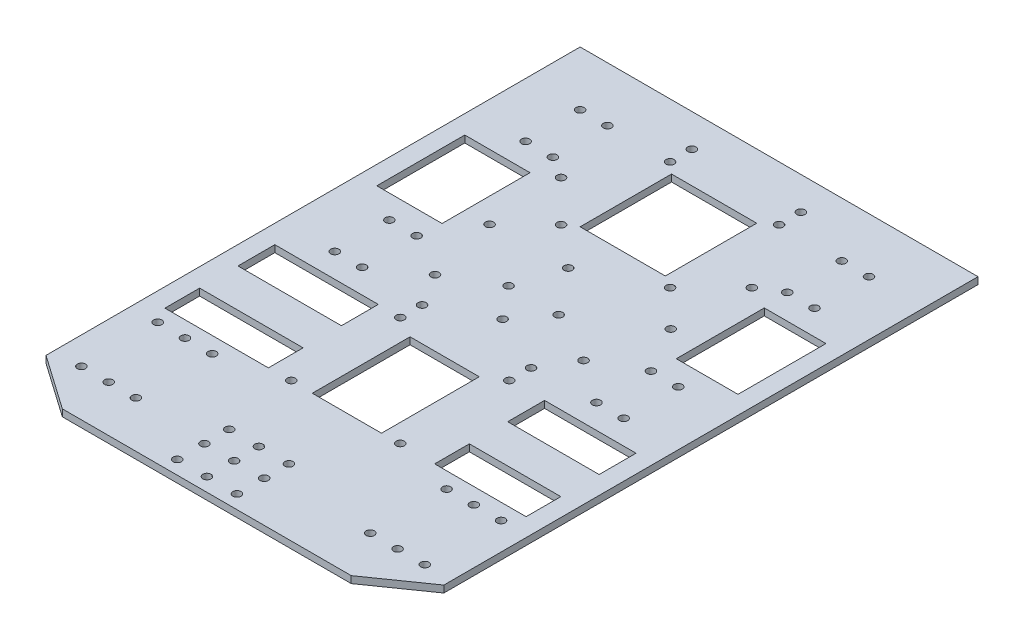
SolidWorks part; units mm, degrees
ref_plane "Front Plane" through (0, 0, 0) normal (0, 0, 1) x (1, 0, 0)
ref_plane "Top Plane" through (0, 0, 0) normal (0, 1, 0) x (1, 0, 0)
ref_plane "Right Plane" through (0, 0, 0) normal (1, 0, 0) x (0, 0, -1)
sketch "Sketch1" plane through (0, 0, 0) normal (0, 1, 0) x (1, 0, 0)
  line L0 (-15.9572, 52.4459) -> (23.1396, 52.4459) construction
  line L1 (-59.5636, 72.4459) -> (86.4364, 72.4459)
  line L2 (-59.5636, 72.4459) -> (-59.5636, -137.5541)
  line L3 (-59.5636, -137.5541) -> (86.4364, -137.5541)
  line L4 (86.4364, 72.4459) -> (86.4364, -137.5541)
  line L5 (27.4909, 27.4459) -> (141.0114, 27.4459) construction
  line L6 (48.4364, 34.6754) -> (48.4364, -17.5836) construction
  line L7 (32.4763, -0.5541) -> (78.64, -0.5541) construction
  line L8 (46.6864, 3.4672) -> (46.6864, -23.1055) construction
  line L9 (-38.1871, -46.5541) -> (45.8207, -46.5541) construction
  line L10 (64.3729, -46.5541) -> (11.2461, -46.5541) construction
  line L11 (-38.1871, -86.5541) -> (70.5809, -86.5541) construction
  line L12 (33.4364, -101.7207) -> (33.4364, -28.4718) construction
  line L13 (-6.5636, -28.4718) -> (-6.5636, -95.9728) construction
  line L14 (13.4364, 100.6324) -> (13.4364, -167.8118) construction
  line L15 (65.0599, -46.5541) -> (-18.9478, -46.5541) construction
  line L16 (50.8131, -17.5541) -> (78.4998, -17.5541) construction
  line L17 (56.4364, -8.3654) -> (56.4364, -40.9131) construction
  line L18 (-45.9412, -92.5541) -> (-11.3599, -92.5541) construction
  line L19 (-49.5636, -76.3375) -> (-49.5636, -109.8295) construction
  line L20 (-59.5636, -123.5541) -> (-39.5636, -137.5541)
  line L21 (86.4364, -123.5541) -> (66.4364, -137.5541)
  line L22 (86.4364, 72.4459) -> (86.4364, -137.5541)
  circle A0 centre (66.4364, 52.4459) radius 1.5
  circle A1 centre (56.4364, 52.4459) radius 1.5
  circle A4 centre (66.4364, 32.4459) radius 1.5
  circle A5 centre (56.4364, 32.4459) radius 1.5
  circle A6 centre (-6.5636, 52.4459) radius 1.5
  circle A7 centre (-6.5636, 12.4459) radius 1.5
  circle A8 centre (33.4364, 52.4459) radius 1.5
  circle A9 centre (33.4364, 12.4459) radius 1.5
  circle A10 centre (-6.5636, 60.4459) radius 1.5
  circle A11 centre (33.4364, 60.4459) radius 1.5
  circle A17 centre (-6.5636, -46.5541) radius 1.5
  circle A18 centre (-6.5636, -86.5541) radius 1.5
  circle A19 centre (33.4364, -46.5541) radius 1.5
  circle A20 centre (33.4364, -86.5541) radius 1.5
  circle A21 centre (-6.5636, -38.5541) radius 1.5
  circle A22 centre (33.4364, -38.5541) radius 1.5
  circle A23 centre (-29.5636, 32.4459) radius 1.5
  circle A24 centre (-39.5636, 52.4459) radius 1.5
  circle A25 centre (-29.5636, 52.4459) radius 1.5
  circle A26 centre (-39.5636, 32.4459) radius 1.5
  circle A27 centre (48.4364, 27.4459) radius 1.5
  circle A28 centre (46.6864, -0.5541) radius 1.5
  circle A29 centre (40.6864, -26.5541) radius 1.5
  circle A30 centre (-13.8136, -26.5541) radius 1.5
  circle A31 centre (-19.8136, -0.5541) radius 1.5
  circle A32 centre (-21.5636, 27.4459) radius 1.5
  circle A34 centre (66.4364, -17.5541) radius 1.5
  circle A35 centre (56.4364, -17.5541) radius 1.5
  circle A36 centre (66.4364, -37.5541) radius 1.5
  circle A37 centre (56.4364, -37.5541) radius 1.5
  circle A38 centre (-39.5636, -17.5541) radius 1.5
  circle A39 centre (-29.5636, -37.5541) radius 1.5
  circle A40 centre (-39.5636, -37.5541) radius 1.5
  circle A41 centre (-29.5636, -17.5541) radius 1.5
  circle A42 centre (-49.5636, -92.5541) radius 1.5
  circle A43 centre (-39.5636, -92.5541) radius 1.5
  circle A44 centre (-29.5636, -92.5541) radius 1.5
  circle A45 centre (-49.5636, -120.5541) radius 1.5
  circle A46 centre (-39.5636, -120.5541) radius 1.5
  circle A47 centre (-29.5636, -120.5541) radius 1.5
  circle A48 centre (76.4364, -120.5541) radius 1.5
  circle A49 centre (66.4364, -120.5541) radius 1.5
  circle A50 centre (56.4364, -120.5541) radius 1.5
  circle A51 centre (56.4364, -92.5541) radius 1.5
  circle A52 centre (66.4364, -92.5541) radius 1.5
  circle A53 centre (76.4364, -92.5541) radius 1.5
  point P60 (-39.5636, 32.4459)
  dimension "D3" = 3
  dimension "D4" = 3
  dimension "D8" = 20
  dimension "D9" = 20
  dimension "D12" = 20
  dimension "D24" = 28
  dimension "D27" = 8
  dimension "D33" = 53
  dimension "D37" = 10
  dimension "D39" = 3
  dimension "D1" = 146
  dimension "D2" = 210
  dimension "D5" = 20
  dimension "D6" = 20
  dimension "D7" = 20
  dimension "D10" = 20
  dimension "D11" = 10
  dimension "D13" = 0
  dimension "D14" = 40
  dimension "D15" = 40
  dimension "D16" = 40
  dimension "D17" = 53
  dimension "D18" = 40
  dimension "D19" = 8
  dimension "D20" = 8
  dimension "D21" = 38
  dimension "D22" = 45
  dimension "D23" = 3.5
  dimension "D25" = 6
  dimension "D26" = 8
  dimension "D28" = 40
  dimension "D29" = 40
  dimension "D30" = 40
  dimension "D31" = 40
  dimension "D32" = 119
  dimension "D34" = 119
  dimension "D35" = 73
  dimension "D36" = 26
  dimension "D38" = 20
  dimension "D40" = 20
  dimension "D41" = 10
  dimension "D42" = 90
  dimension "D43" = 165
  dimension "D44" = 10
  dimension "D45" = 10
  dimension "D46" = 10
  dimension "D47" = 28
  dimension "D48" = 14
  dimension "D49" = 20
extrude "Boss-Extrude1" add sketch "Sketch1" along normal blind 2.54 contours L21 L4 L1 L2 L20 L3 A53 A52 A51 A50 A49 A48 A46 A44 A42 A40 A38 A37 A36 A35 A34 A31 A26 A24 A0 A1 A4 A5
sketch "Sketch3" plane through (0, 2.54, 0) normal (0, 1, 0) x (1, 0, 0)
  line L0 (-39.5636, -137.5541) -> (66.4364, -137.5541) construction
  line L2 (-52.747, -46.4012) -> (-14.7812, -46.4012)
  line L3 (-52.747, -46.4012) -> (-52.747, -86.7398)
  line L4 (-52.747, -86.7398) -> (-14.7812, -86.7398)
  line L5 (-14.7812, -46.4012) -> (-14.7812, -86.7398)
  line L6 (46.2352, -46.4012) -> (79.7942, -46.4012)
  line L7 (46.2352, -46.4012) -> (46.2352, -86.7398)
  line L8 (46.2352, -86.7398) -> (79.7942, -86.7398)
  line L9 (79.7942, -46.4012) -> (79.7942, -86.7398)
  line L10 (-52.747, 23.2992) -> (-28.7966, 23.2992)
  line L11 (-52.747, 23.2992) -> (-52.747, -8.9831)
  line L12 (-52.747, -8.9831) -> (-28.7966, -8.9831)
  line L13 (-28.7966, 23.2992) -> (-28.7966, -8.9831)
  line L14 (57.155, 23.2992) -> (79.7942, 23.2992)
  line L15 (57.155, 23.2992) -> (57.155, -8.9831)
  line L16 (57.155, -8.9831) -> (79.7942, -8.9831)
  line L17 (79.7942, 23.2992) -> (79.7942, -8.9831)
  line L18 (-2.4131, 48.8348) -> (28.8491, 48.8348)
  line L19 (-2.4131, 48.8348) -> (-2.4131, 15.296)
  line L20 (-2.4131, 15.296) -> (28.8491, 15.296)
  line L21 (28.8491, 48.8348) -> (28.8491, 15.296)
  line L22 (1.3401, -50.8687) -> (26.7352, -50.8687)
  line L23 (1.3401, -50.8687) -> (1.3401, -86.7398)
  line L24 (1.3401, -86.7398) -> (26.7352, -86.7398)
  line L25 (26.7352, -50.8687) -> (26.7352, -86.7398)
  circle A0 centre (-2.4131, -132.5541) radius 1.5
  circle A1 centre (8.4792, -132.5541) radius 1.5
  circle A2 centre (8.4792, 0) radius 1.5
  circle A3 centre (8.4792, 0) radius 1.5
  circle A4 centre (19.5093, -132.5541) radius 1.5
  circle A5 centre (-2.4131, -122.5541) radius 1.5
  circle A6 centre (8.4792, -122.5541) radius 1.5
  circle A7 centre (19.5093, -122.5541) radius 1.5
  circle A8 centre (-2.4131, -113.4706) radius 1.5
  circle A9 centre (8.4792, -113.4706) radius 1.5
  circle A10 centre (19.5093, -113.4706) radius 1.5
  circle A11 centre (3.2097, -16.5932) radius 1.5
  circle A12 centre (21.5938, -16.5932) radius 1.5
  circle A13 centre (12.7134, -28.2781) radius 1.5
  dimension "D1" = 3
  dimension "D2" = 5
  dimension "D3" = 10
extrude "Cut-Extrude1" cut sketch "Sketch3" against normal blind 2.54 contours L21 L18 L19 L20 | L13 L10 L11 L12 | L5 L2 L3 L4 | L25 L22 L23 L24 | L9 L6 L7 L8 | L17 L14 L15 L16 | A11 | A13 | A12 | A2 | A8 | A9 | A10 | A7 | A5 | A6 | A1 | A0 | A4
sketch "Sketch4" plane through (0, 0, 0) normal (0, 1, 0) x (1, 0, 0)
  line L0 (-52.747, -46.4012) -> (-52.747, -86.7398) construction
  line L1 (-14.7812, -46.4012) -> (-14.7812, -86.7398) construction
  line L2 (-52.747, -59.9364) -> (-14.7812, -59.9364)
  line L3 (-52.747, -59.9364) -> (-52.747, -73.9937)
  line L4 (-52.747, -73.9937) -> (-14.7812, -73.9937)
  line L5 (-14.7812, -59.9364) -> (-14.7812, -73.9937)
  line L6 (46.2352, -46.4012) -> (46.2352, -86.7398) construction
  line L7 (46.2352, -59.9364) -> (79.7942, -59.9364)
  line L8 (46.2352, -59.9364) -> (46.2352, -73.9937)
  line L9 (46.2352, -73.9937) -> (79.7942, -73.9937)
  line L10 (79.7942, -59.9364) -> (79.7942, -73.9937)
  line L11 (79.7942, -46.4012) -> (79.7942, -86.7398) construction
extrude "Boss-Extrude2" add sketch "Sketch4" along normal blind 2.54
